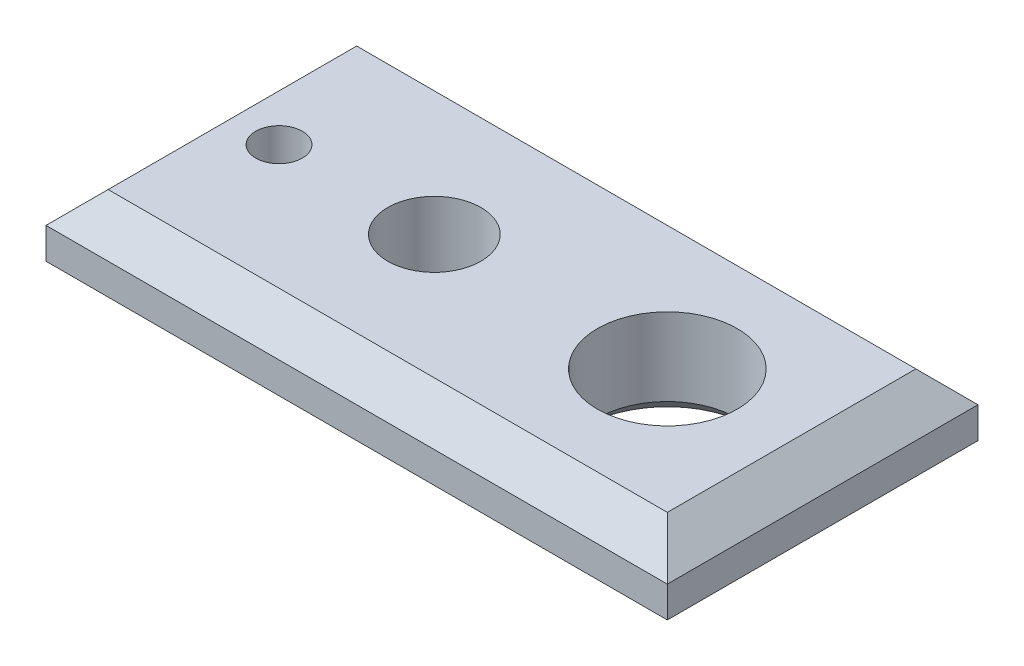
SolidWorks part; units mm, degrees
material "AISI 1020"
ref_plane "Front Plane" through (0, 0, 0) normal (0, 0, 1) x (1, 0, 0)
ref_plane "Top Plane" through (0, 0, 0) normal (0, 1, 0) x (1, 0, 0)
ref_plane "Right Plane" through (0, 0, 0) normal (1, 0, 0) x (0, 0, -1)
sketch "Sketch1" plane through (0, 0, 0) normal (0, 1, 0) x (1, 0, 0)
  line L0 (-138.1766, 0) -> (155.5556, 0) construction
  line L1 (100, -50) -> (-100, -50)
  line L2 (100, -50) -> (100, 50)
  line L3 (100, 50) -> (-100, 50)
  line L4 (-100, -50) -> (-100, 50)
  circle A0 centre (-75, 0) radius 7.5
  circle A1 centre (-25, 0) radius 15
  circle A2 centre (50, 0) radius 22.5
  point P0 (0, 0)
  dimension "D6" = 15
  dimension "D7" = 30
  dimension "D8" = 45
  dimension "D1" = 200
  dimension "D2" = 100
  dimension "D3" = 25
  dimension "D4" = 50
  dimension "D5" = 75
extrude "Boss-Extrude2" add sketch "Sketch1" along normal blind 30
chamfer "Chamfer1" distance 10 angle 45 4 edges at (0, 30, -50) (-100, 30, 0) (0, 30, 50) (100, 30, 0)
chamfer "Chamfer4" distance 5 angle 45 3 edges at (50, 0, 22.5) (-25, 0, 15) (-75, 0, 7.5)
chamfer "Chamfer5" distance 10 angle 45 4 edges at (-100, 0, 0) (0, 0, -50) (100, 0, 0) (0, 0, 50)
